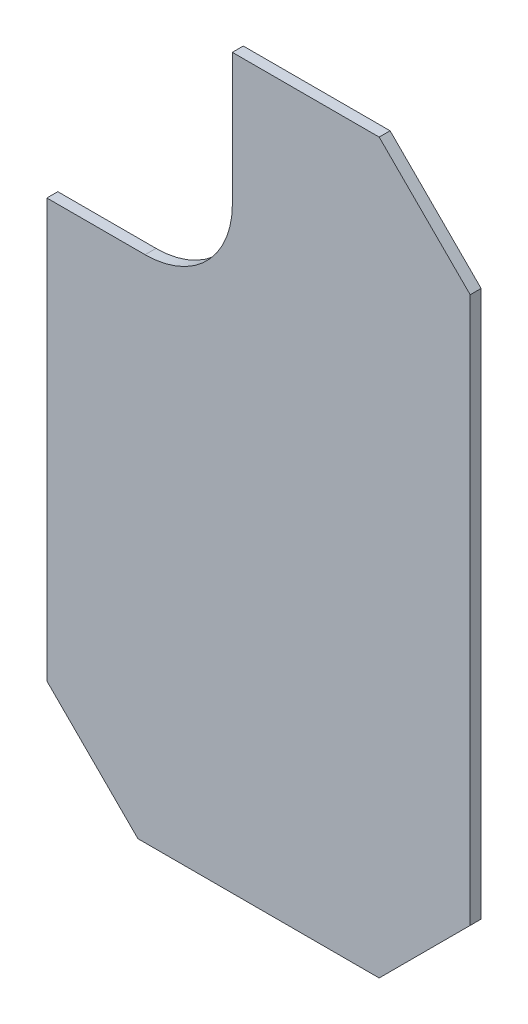
SolidWorks part; units mm, degrees
material "EPDM 60 Durometer"
ref_plane "Front Plane" through (0, 0, 0) normal (0, 0, 1) x (1, 0, 0)
ref_plane "Top Plane" through (0, 0, 0) normal (0, 1, 0) x (1, 0, 0)
ref_plane "Right Plane" through (0, 0, 0) normal (1, 0, 0) x (0, 0, -1)
sketch "Sketch1" plane through (0, 0, 0) normal (0, 0, 1) x (1, 0, 0)
  line L0 (-44.8225, -51.3161) -> (-44.8225, -89.4161) construction
  line L1 (-51.1725, -95.7661) -> (-68, -95.7661) construction
  line L2 (-68, -95.7661) -> (-74.35, -89.4161) construction
  line L3 (-74.35, -89.4161) -> (-74.35, -60.9967) construction
  line L4 (-73.588, -60.2347) -> (-67.5, -60.2347) construction
  line L5 (-61.4125, -54.1472) -> (-61.4125, -45.7281) construction
  line L6 (-60.6505, -44.9661) -> (-51.1725, -44.9661) construction
  line L7 (-51.1725, -44.9661) -> (-44.8225, -51.3161) construction
  line L8 (-44.8225, -89.4161) -> (-51.1725, -95.7661) construction
  line L9 (-51.1725, -95.7661) -> (-68, -95.7661)
  line L10 (-68, -95.7661) -> (-74.35, -89.4161)
  line L11 (-74.35, -89.4161) -> (-74.35, -60.2347)
  line L12 (-74.35, -60.2347) -> (-67.5, -60.2347)
  line L13 (-61.4125, -54.1472) -> (-61.4125, -44.9661)
  line L14 (-61.4125, -44.9661) -> (-51.1725, -44.9661)
  line L15 (-51.1725, -44.9661) -> (-44.8225, -51.3161)
  line L16 (-44.8225, -51.3161) -> (-44.8225, -89.4161)
  line L17 (-44.8225, -89.4161) -> (-51.1725, -95.7661)
  arc A0 (-67.5, -60.2347) -> (-61.4125, -54.1472) centre (-67.5, -54.1472) ccw construction
  arc A1 (-67.5, -60.2347) -> (-61.4125, -54.1472) centre (-67.5, -54.1472) ccw
  point P0 (-61.3162, -44.9661)
extrude "Boss-Extrude1" add sketch "Sketch1" along normal blind 0.762
